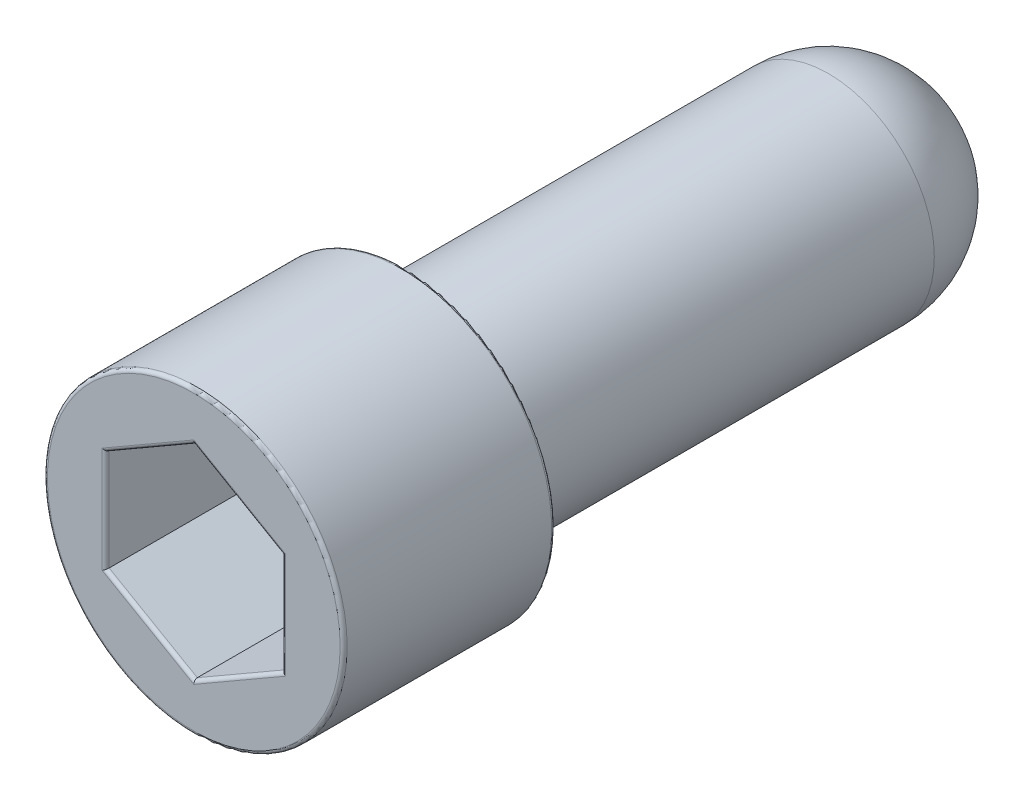
SolidWorks part; units mm, degrees
ref_plane "Front Plane" through (0, 0, 0) normal (0, 0, 1) x (1, 0, 0)
ref_plane "Top Plane" through (0, 0, 0) normal (0, 1, 0) x (1, 0, 0)
ref_plane "Right Plane" through (0, 0, 0) normal (1, 0, 0) x (0, 0, -1)
sketch "Sketch1" plane through (0, 0, 0) normal (0, 0, 1) x (1, 0, 0)
  circle A0 centre (0, 0) radius 4.25
  dimension "D1" = 8.5
extrude "Boss-Extrude1" add sketch "Sketch1" along normal blind 6
sketch "Sketch2" plane through (0, 0, 6) normal (0, 0, 1) x (1, 0, 0)
  line L1 (0, 2.8868) -> (-2.5, 1.4434)
  line L2 (-2.5, 1.4434) -> (-2.5, -1.4434)
  line L3 (-2.5, -1.4434) -> (0, -2.8868)
  line L4 (0, -2.8868) -> (2.5, -1.4434)
  line L5 (2.5, -1.4434) -> (2.5, 1.4434)
  line L6 (2.5, 1.4434) -> (0, 2.8868)
  circle A0 centre (0, 0) radius 2.5 construction
  dimension "D1" = 5
extrude "Cut-Extrude1" cut sketch "Sketch2" against normal blind 4
sketch "Sketch3" plane through (0, 0, 0) normal (0, 0, -1) x (-1, 0, 0)
  circle A0 centre (0, 0) radius 3
  dimension "D1" = 6
extrude "Boss-Extrude2" add sketch "Sketch3" along normal blind 15
fillet "Fillet1" radius 0.1 8 edges at (1.25, 2.1651, 6) (2.5, 0, 6) (1.25, -2.1651, 6) (-1.25, -2.1651, 6) (-2.5, 0, 6) (-1.25, 2.1651, 6) (4.25, 0, 6) (4.25, 0, 0)
fillet "Fillet2" radius 3 1 edges at (-3, 0, -15)
